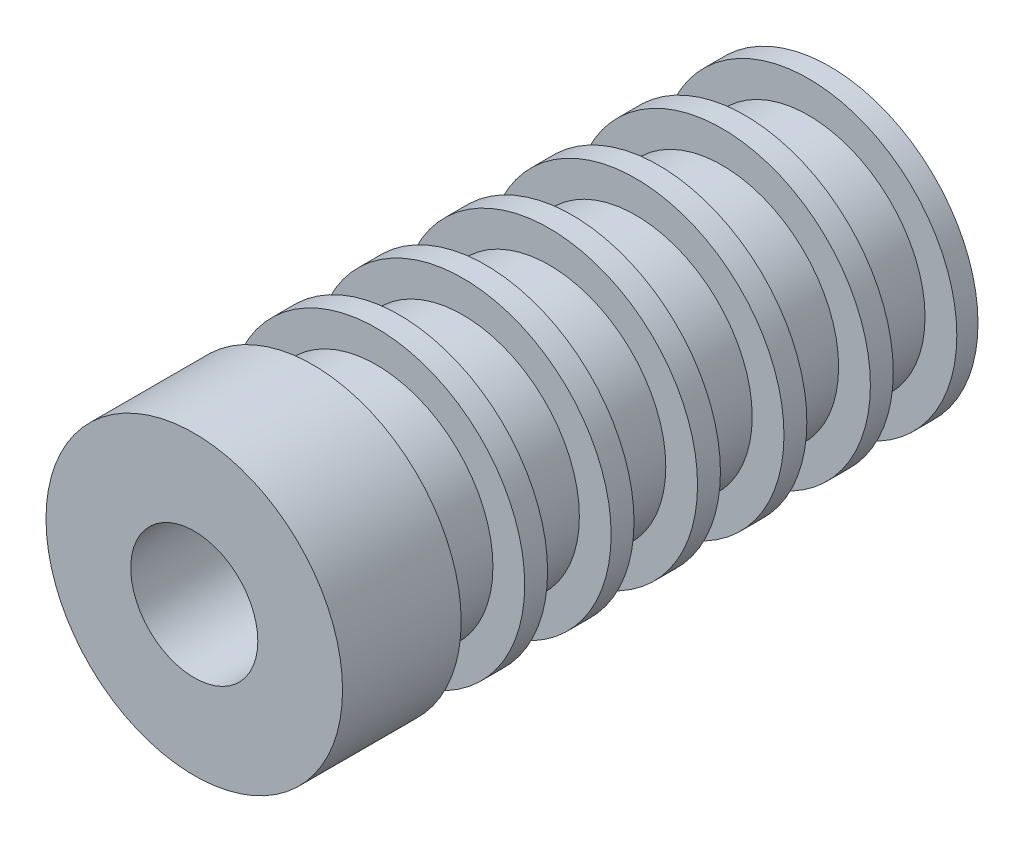
SolidWorks part; units mm, degrees
material "AISI 304"
ref_plane "Front Plane" through (0, 0, 0) normal (0, 0, 1) x (1, 0, 0)
ref_plane "Top Plane" through (0, 0, 0) normal (0, 1, 0) x (1, 0, 0)
ref_plane "Right Plane" through (0, 0, 0) normal (1, 0, 0) x (0, 0, -1)
sketch "Sketch1" plane through (0, 0, 0) normal (0, 0, 1) x (1, 0, 0)
  circle A0 centre (0, 0) radius 11.1125
  circle A1 centre (0, 0) radius 3.2004
  dimension "OD" = 22.225
  dimension "ID" = 6.4008
extrude "Extrude1" add sketch "Sketch1" along normal mid plane 50.8
sketch "Sketch2" plane through (0, 0, 0) normal (1, 0, 0) x (0, 0, -1)
  line L0 (-25.4, -3.2004) -> (25.4, -3.2004) construction
  line L3 (25.4, 3.2004) -> (-25.4, 3.2004) construction
  line L5 (-25.4, -3.2004) -> (25.4, -3.2004)
  line L6 (25.4, 3.2004) -> (-25.4, 3.2004)
sketch "Sketch4" plane through (0, 0, 25.4) normal (0, 0, 1) x (1, 0, 0)
  line L0 (0, 0) -> (-2.263, 2.263)
  line L1 (0, -12.2237) -> (0, 12.2237) construction
  circle A0 centre (0, 0) radius 3.2004 construction
  dimension "D1" = 45
sketch "Sketch5" plane through (0, 0, 25.4) normal (0, 0, 1) x (1, 0, 0)
  circle A0 centre (0, 0) radius 3.2004 construction
  circle A1 centre (0, 0) radius 11.1125
  circle A2 centre (0, 0) radius 11.1125
  circle A3 centre (0, 0) radius 3.2004
  dimension "D1" = 0
extrude "Cut-Extrude1" cut sketch "Sketch5" against normal blind 3.175
sketch "Sketch6" plane through (0, 0, 22.225) normal (0, 0, 1) x (1, 0, 0)
  circle A0 centre (0, 0) radius 4.7625
  dimension "D1" = 9.525
extrude "Cut-Extrude2" cut sketch "Sketch6" against normal through all
sketch "Sketch7" plane through (0, 0, -25.4) normal (0, 0, -1) x (-1, 0, 0)
  circle A0 centre (0, 0) radius 8.7312
  circle A1 centre (0, 0) radius 11.1125 construction
  circle A2 centre (0, 0) radius 11.1125
  dimension "D1" = 17.4625
extrude "Cut-Extrude3" cut sketch "Sketch7" against normal blind 4.7625 from offset 1.5875 offset against normal yes
pattern_linear "LPattern1" count 6 spacing 6.477 along (0, 0, 1) of "Cut-Extrude3"
